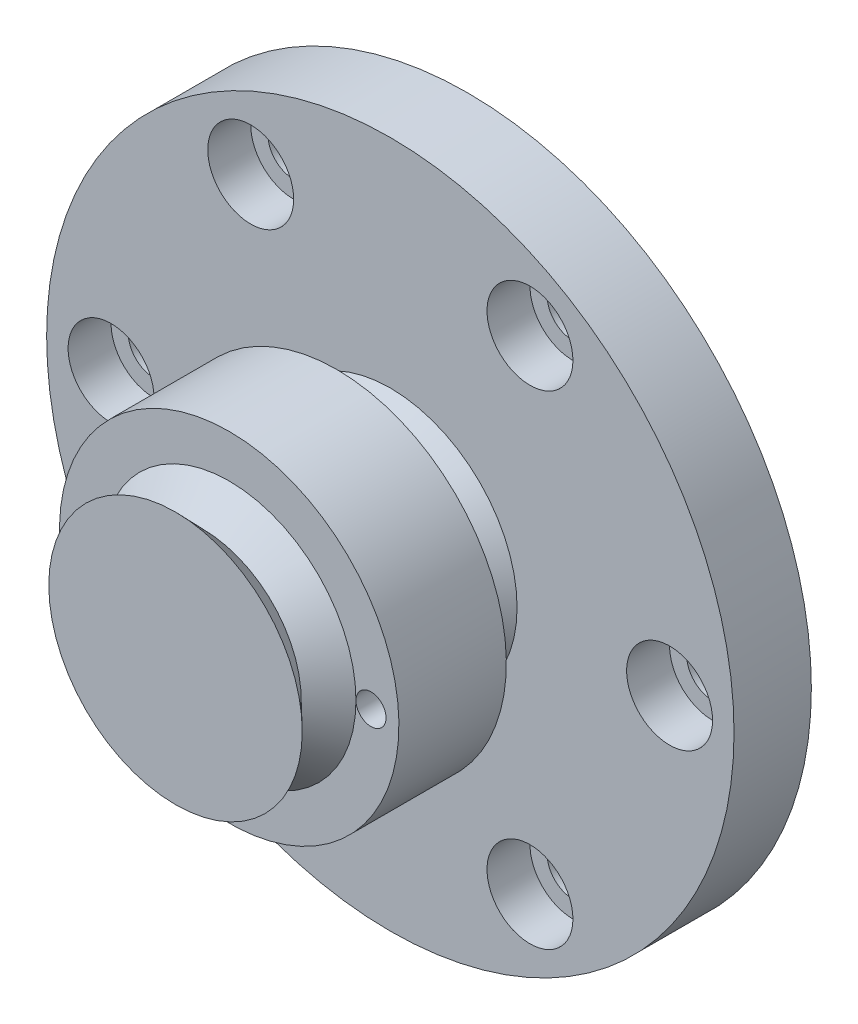
SolidWorks part; units mm, degrees
ref_plane "정면" through (0, 0, 0) normal (0, 0, 1) x (1, 0, 0)
ref_plane "윗면" through (0, 0, 0) normal (0, 1, 0) x (1, 0, 0)
ref_plane "우측면" through (0, 0, 0) normal (1, 0, 0) x (0, 0, -1)
sketch "스케치1" plane through (0, 0, 0) normal (0, 0, 1) x (1, 0, 0)
  circle A0 centre (0, 0) radius 16
  circle A1 centre (13, 0) radius 1.2
  circle A2 centre (6.5, -11.2583) radius 1.2
  circle A3 centre (-6.5, -11.2583) radius 1.2
  circle A4 centre (-13, 0) radius 1.2
  circle A5 centre (-6.5, 11.2583) radius 1.2
  circle A6 centre (6.5, 11.2583) radius 1.2
  point P6 (0, 0)
  point P17 (0, 0)
  dimension "D1" = 2.4
  dimension "D2" = 32
  dimension "D3" = 13
  dimension "D4" = 6
extrude "보스-돌출1" add sketch "스케치1" along normal blind 3.6
sketch "스케치2" plane through (0, 0, 3.6) normal (0, 0, 1) x (1, 0, 0)
  circle A0 centre (13, 0) radius 2
  circle A1 centre (6.5, -11.2583) radius 2
  circle A2 centre (-6.5, -11.2583) radius 2
  circle A3 centre (-13, 0) radius 2
  circle A4 centre (-6.5, 11.2583) radius 2
  circle A5 centre (6.5, 11.2583) radius 2
  point P15 (0, 0)
  dimension "D1" = 4
  dimension "D2" = 6
extrude "컷-돌출1" cut sketch "스케치2" against normal blind 2
sketch "스케치3" plane through (0, 0, 0) normal (0, 0, -1) x (-1, 0, 0)
  circle A0 centre (-6, 0) radius 1
  circle A1 centre (6, 0) radius 1
  dimension "D1" = 2
  dimension "D3" = 2
  dimension "D2" = 6
  dimension "D4" = 6
extrude "컷-돌출2" cut sketch "스케치3" against normal blind 2
sketch "스케치4" plane through (0, 0, 3.6) normal (0, 0, 1) x (1, 0, 0)
  circle A0 centre (0, 0) radius 7.9
  dimension "D1" = 15.8
extrude "보스-돌출2" add sketch "스케치4" along normal blind 10
sketch "스케치5" plane through (0, 0, 0) normal (1, 0, 0) x (0, 0, -1)
  line L0 (-13.6, 7.9) -> (-13.6, 5.9)
  line L2 (-13.6, 7.9) -> (-13.6, -7.9) construction
  line L3 (-13.6, 5.9) -> (-12.35, 4.6)
  line L4 (-12.35, 4.6) -> (-11.1, 5.9)
  line L6 (-11.1, 5.9) -> (-11.1, 7.9)
  line L7 (-3.6, 7.9) -> (-13.6, 7.9) construction
  line L8 (0, 0) -> (-8.9478, 0) construction
  line L9 (-11.1, 7.9) -> (-13.6, 7.9)
  line L10 (-6.1, 7.9) -> (-3.6, 7.9)
  line L11 (-3.6, 16) -> (-3.6, -16) construction
  line L12 (-3.6, 7.9) -> (-3.6, 5.9)
  line L13 (-3.6, 7.9) -> (-3.6, -7.9) construction
  line L14 (-3.6, 5.9) -> (-4.85, 4.6)
  line L15 (-4.85, 4.6) -> (-6.1, 5.9)
  line L16 (-6.1, 5.9) -> (-6.1, 7.9)
  dimension "D1" = 2.5
  dimension "D2" = 2.5
  dimension "D3" = 2
  dimension "D4" = 1.3
  dimension "D5" = 1.25
  dimension "D6" = 2
  dimension "D7" = 2
  dimension "D8" = 1.25
  dimension "D9" = 1.3
  dimension "D10" = 2
revolve "컷-회전1" cut sketch "스케치5" angle 360 about L8
sketch "스케치6" plane through (0, 0, 11.1) normal (0, 0, 1) x (1, 0, 0)
  circle A0 centre (6.6, 0) radius 0.7
  dimension "D1" = 1.4
  dimension "D2" = 6.6
extrude "컷-돌출3" cut sketch "스케치6" against normal up to surface (5 mm away) up to face at (0, 5.9, 6.1)
